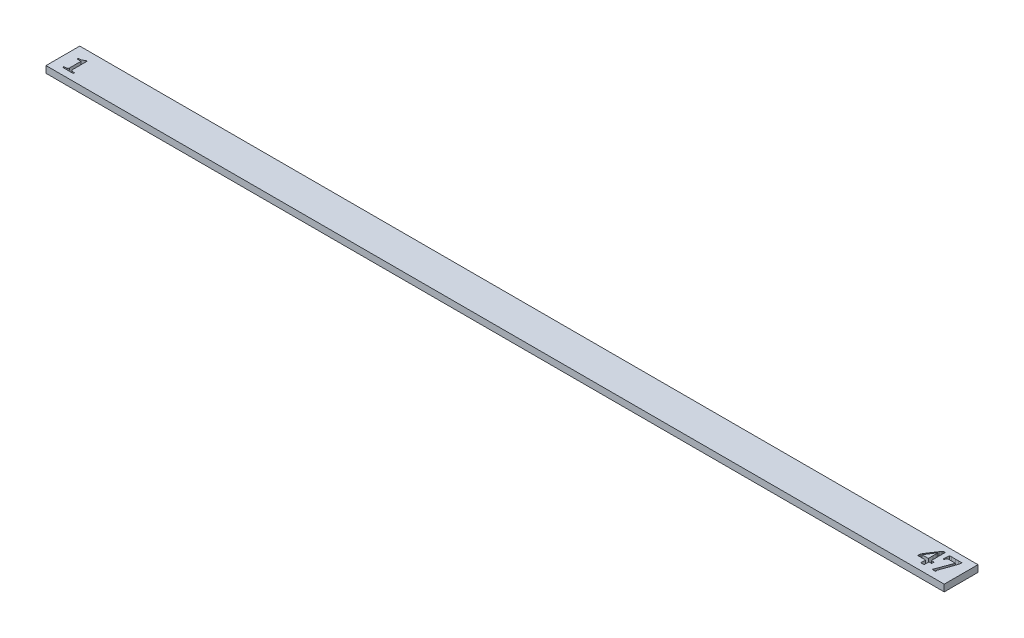
SolidWorks part; units mm, degrees
ref_plane "Front Plane" through (0, 0, 0) normal (0, 0, 1) x (1, 0, 0)
ref_plane "Top Plane" through (0, 0, 0) normal (0, 1, 0) x (1, 0, 0)
ref_plane "Right Plane" through (0, 0, 0) normal (1, 0, 0) x (0, 0, -1)
sketch "Sketch1" plane through (0, 0, 0) normal (0, 1, 0) x (1, 0, 0)
  line L1 (0, 0) -> (399, 0)
  line L2 (0, 0) -> (0, 15)
  line L3 (0, 15) -> (399, 15)
  line L4 (399, 0) -> (399, 15)
  dimension "D1" = 399
  dimension "D2" = 15
extrude "Boss-Extrude1" add sketch "Sketch1" along normal blind 3 contours L2 L1 L4 L3
sketch "Sketch3" plane through (0, 3, 0) normal (0, 1, 0) x (1, 0, 0)
  line L0 (0, 3) -> (399, 3)
  line L1 (0, 0) -> (0, 15) construction
  line L2 (399, 0) -> (399, 15) construction
  line L3 (0, 0) -> (399, 0) construction
  line L4 (390.1574, 12.1343) -> (391.8617, 12.1196)
  line L5 (391.8617, 12.1196) -> (393.3036, 12.1343)
  line L6 (393.3036, 12.1343) -> (394.1306, 12.1343)
  line L7 (394.1306, 12.1343) -> (394.416, 12.1343)
  line L8 (393.291, 7.2481) -> (392.9405, 6.2512)
  line L9 (392.6047, 5.3193) -> (392.0317, 3.7031)
  line L10 (392.0968, 2.7313) -> (391.9142, 2.7313)
  line L11 (391.9142, 2.7313) -> (391.3874, 2.7397)
  line L12 (391.507, 5.3046) -> (392.7642, 8.6943)
  line L13 (392.7642, 8.6943) -> (393.0791, 9.559)
  line L14 (392.2899, 10.5224) -> (391.2341, 10.5056)
  line L15 (391.2341, 10.5056) -> (390.3904, 10.5224)
  line L16 (388.2537, 6.2239) -> (388.2537, 5.1493)
  line L17 (387.0448, 4.9415) -> (387.0448, 4.5133)
  line L18 (387.0448, 4.5133) -> (387.0448, 4.0557)
  line L19 (387.0448, 4.0557) -> (387.0448, 3.7409)
  line L20 (387.0448, 2.7313) -> (386.4403, 2.7313)
  line L21 (386.4403, 2.7313) -> (386.0667, 2.7313)
  line L22 (385.8421, 2.7313) -> (385.7225, 2.7313)
  line L23 (385.5672, 2.7313) -> (385.5672, 4.1187)
  line L24 (385.5672, 4.1187) -> (385.5672, 5.0128)
  line L25 (384.5408, 5.1493) -> (384.0686, 5.1493)
  line L26 (382.0746, 5.1493) -> (382.0746, 5.2206)
  line L27 (382.0746, 5.2206) -> (382.0746, 5.6719)
  line L28 (382.0746, 5.6719) -> (382.0746, 5.8167)
  line L29 (382.0746, 5.8167) -> (382.0746, 6.0854)
  line L30 (382.0746, 6.0854) -> (382.0746, 6.1378)
  line L31 (382.4944, 6.9984) -> (384.1504, 9.559)
  line L32 (387.0448, 12.382) -> (387.0448, 12.2938)
  line L33 (387.0448, 12.2938) -> (387.0448, 11.746)
  line L34 (387.0448, 11.746) -> (387.0448, 11.555)
  line L35 (387.0448, 11.555) -> (387.0448, 11.2507)
  line L36 (387.0448, 11.2507) -> (387.0448, 10.9485)
  line L37 (387.0448, 10.9485) -> (387.0448, 10.216)
  line L38 (387.0448, 10.216) -> (387.0448, 9.899)
  line L39 (387.0448, 9.899) -> (387.0448, 9.4834)
  line L40 (387.0448, 9.4834) -> (387.0448, 9.0993)
  line L41 (387.0448, 9.0993) -> (387.0448, 8.5746)
  line L42 (387.0448, 8.5746) -> (387.0448, 8.073)
  line L43 (387.0448, 8.073) -> (387.0448, 7.4874)
  line L44 (387.0448, 7.4874) -> (387.0448, 6.2239)
  line L45 (387.7059, 6.2239) -> (387.8885, 6.2239)
  line L46 (385.5672, 7.4307) -> (385.5672, 7.9953)
  line L47 (385.5672, 7.9953) -> (385.5672, 8.4802)
  line L48 (385.5672, 8.4802) -> (385.5735, 9.7332)
  line L49 (385.5735, 9.7332) -> (385.5672, 10.3062)
  line L50 (384.5933, 9.2778) -> (383.9489, 8.2346)
  line L51 (383.1283, 6.3582) -> (383.4788, 6.3582)
  line L52 (383.4788, 6.3582) -> (384.1777, 6.3582)
  line L53 (384.1777, 6.3582) -> (385.1516, 6.3582)
  line L54 (385.1516, 6.3582) -> (385.5672, 6.3582)
  spline S0 degree 3 poles (389.2885, 12.1343) (389.4074, 12.1343) (389.6971, 12.1343) (389.9867, 12.1343) (390.1574, 12.1343) knots 0 0 0 0 0.410628 1 1 1 1
  spline S1 degree 2 poles (394.416, 12.1343) (394.5483, 12.1343) (394.6805, 12.1343) knots 0 0 0 1 1 1
  spline S2 degree 2 poles (394.6805, 12.1343) (394.7016, 11.9249) (394.7015, 11.7146) knots 0 0 0 1 1 1
  spline S3 degree 3 poles (394.7015, 11.7146) (394.7031, 11.6686) (394.6907, 11.5918) (394.6741, 11.4778) (394.6522, 11.3659) (394.6251, 11.2364) (394.5773, 11.0283) (394.5357, 10.8643) (394.5063, 10.7491) knots 0 0 0 0 0.13905 0.235946 0.350701 0.485483 0.638259 1 1 1 1
  spline S4 degree 3 poles (394.5063, 10.7491) (394.3713, 10.3858) (394.2226, 9.9355) (394.055, 9.4149) (393.9732, 9.1593) (393.9146, 8.9873) (393.8766, 8.8853) knots 0 0 0 0 0.590758 0.723007 0.834001 1 1 1 1
  spline S5 degree 3 poles (393.8766, 8.8853) (393.8139, 8.7235) (393.7049, 8.4219) (393.6038, 8.1175) (393.5618, 7.9764) knots 0 0 0 0 0.54115 1 1 1 1
  spline S6 degree 3 poles (393.5618, 7.9764) (393.5158, 7.8672) (393.4261, 7.6242) (393.3365, 7.3811) (393.291, 7.2481) knots 0 0 0 0 0.457479 1 1 1 1
  spline S7 degree 3 poles (392.9405, 6.2512) (392.9019, 6.129) (392.7893, 5.8185) (392.6773, 5.5079) (392.6047, 5.3193) knots 0 0 0 0 0.387978 1 1 1 1
  spline S8 degree 2 poles (392.0317, 3.7031) (391.9708, 3.5883) (391.9583, 3.4597) knots 0 0 0 1 1 1
  spline S9 degree 3 poles (391.9583, 3.4597) (391.9594, 3.4188) (391.9839, 3.3553) (392.0515, 3.2864) (392.1193, 3.235) (392.1889, 3.1853) (392.257, 3.1186) (392.2825, 3.0565) (392.2836, 3.0168) knots 0 0 0 0 0.21312 0.343422 0.503307 0.660927 0.793754 1 1 1 1
  spline S10 degree 3 poles (392.2836, 3.0168) (392.2823, 2.9669) (392.2381, 2.8546) (392.1492, 2.7737) (392.0968, 2.7313) knots 0 0 0 0 0.419347 1 1 1 1
  spline S11 degree 3 poles (391.3874, 2.7397) (391.3602, 2.7429) (391.309, 2.7411) (391.2271, 2.7429) (391.065, 2.7317) (390.9263, 2.7344) (390.8186, 2.7313) knots 0 0 0 0 0.143976 0.269387 0.431851 1 1 1 1
  spline S12 degree 2 poles (390.8186, 2.7313) (390.6779, 2.7313) (390.5373, 2.7313) knots 0 0 0 1 1 1
  spline S13 degree 3 poles (390.5373, 2.7313) (390.5497, 2.8378) (390.636, 3.1077) (390.7523, 3.3648) (390.8249, 3.5247) knots 0 0 0 0 0.377761 1 1 1 1
  spline S14 degree 3 poles (390.8249, 3.5247) (390.8592, 3.6042) (390.917, 3.7399) (390.9975, 3.9457) (391.0768, 4.1509) (391.1699, 4.3903) (391.3144, 4.7787) (391.4266, 5.0879) (391.507, 5.3046) knots 0 0 0 0 0.13619 0.232079 0.347806 0.482346 0.636339 1 1 1 1
  spline S15 degree 3 poles (393.0791, 9.559) (393.1161, 9.6353) (393.1856, 9.8169) (393.2493, 10.0004) (393.2826, 10.1047) knots 0 0 0 0 0.436195 1 1 1 1
  spline S16 degree 3 poles (393.2826, 10.1047) (393.2964, 10.1557) (393.3489, 10.2789) (393.3843, 10.4082) (393.417, 10.4825) knots 0 0 0 0 0.394055 1 1 1 1
  spline S17 degree 3 poles (393.417, 10.4825) (393.2072, 10.4941) (392.8316, 10.5116) (392.4558, 10.5235) (392.2899, 10.5224) knots 0 0 0 0 0.558859 1 1 1 1
  spline S18 degree 3 poles (390.3904, 10.5224) (390.2795, 10.5191) (390.1233, 10.5162) (389.9439, 10.4576) (389.8479, 10.402) (389.7801, 10.3185) (389.7259, 10.2157) (389.6823, 10.0881) (389.6537, 9.9447) (389.6276, 9.8052) (389.598, 9.6861) (389.5621, 9.5983) (389.5277, 9.5316) (389.4769, 9.4939) (389.3959, 9.4512) (389.3197, 9.4525) (389.2696, 9.4478) knots 0 0 0 0 0.189213 0.259177 0.317619 0.373826 0.438412 0.513621 0.600884 0.685342 0.753932 0.807539 0.846294 0.87826 0.912652 1 1 1 1
  spline S19 degree 3 poles (389.2696, 9.4478) (389.2096, 9.4441) (389.0726, 9.511) (389.0612, 9.6645) (389.0597, 9.7332) knots 0 0 0 0 0.447089 1 1 1 1
  spline S20 degree 3 poles (389.0597, 9.7332) (389.0577, 9.8826) (389.0859, 10.2424) (389.1123, 10.6021) (389.1395, 10.812) knots 0 0 0 0 0.413664 1 1 1 1
  spline S21 degree 3 poles (389.1395, 10.812) (389.1743, 11.0497) (389.212, 11.4917) (389.2566, 11.9331) (389.2885, 12.1343) knots 0 0 0 0 0.541005 1 1 1 1
  spline S22 degree 3 poles (388.2537, 5.1493) (388.1313, 5.1493) (387.9158, 5.1493) (387.7003, 5.1493) (387.6073, 5.1493) knots 0 0 0 0 0.568182 1 1 1 1
  spline S23 degree 2 poles (387.6073, 5.1493) (387.326, 5.1493) (387.0448, 5.1493) knots 0 0 0 1 1 1
  spline S24 degree 3 poles (387.0448, 5.1493) (387.0448, 5.1031) (387.0448, 5.0338) (387.0448, 4.9646) (387.0448, 4.9415) knots 0 0 0 0 0.666667 1 1 1 1
  spline S25 degree 3 poles (387.0448, 3.7409) (387.0448, 3.6905) (387.0448, 3.5471) (387.0448, 3.4037) (387.0448, 3.3106) knots 0 0 0 0 0.35122 1 1 1 1
  spline S26 degree 3 poles (387.0448, 3.3106) (387.0448, 3.2302) (387.0448, 3.0371) (387.0448, 2.844) (387.0448, 2.7313) knots 0 0 0 0 0.416667 1 1 1 1
  spline S27 degree 2 poles (386.0667, 2.7313) (385.9544, 2.7313) (385.8421, 2.7313) knots 0 0 0 1 1 1
  spline S28 degree 2 poles (385.7225, 2.7313) (385.6448, 2.7313) (385.5672, 2.7313) knots 0 0 0 1 1 1
  spline S29 degree 2 poles (385.5672, 5.0128) (385.5672, 5.081) (385.5672, 5.1493) knots 0 0 0 1 1 1
  spline S30 degree 3 poles (385.5672, 5.1493) (385.4244, 5.1493) (385.0823, 5.1493) (384.7402, 5.1493) (384.5408, 5.1493) knots 0 0 0 0 0.417178 1 1 1 1
  spline S31 degree 2 poles (384.0686, 5.1493) (383.3906, 5.1493) (382.7127, 5.1493) knots 0 0 0 1 1 1
  spline S32 degree 3 poles (382.7127, 5.1493) (382.6476, 5.1493) (382.5448, 5.1493) (382.4419, 5.1493) (382.4042, 5.1493) knots 0 0 0 0 0.632653 1 1 1 1
  spline S33 degree 2 poles (382.4042, 5.1493) (382.2394, 5.1493) (382.0746, 5.1493) knots 0 0 0 1 1 1
  spline S34 degree 3 poles (382.0746, 6.1378) (382.1238, 6.2444) (382.1936, 6.3963) (382.2862, 6.5855) (382.3422, 6.7026) (382.3904, 6.8013) (382.4392, 6.8983) (382.4714, 6.9628) (382.4944, 6.9984) knots 0 0 0 0 0.367667 0.523514 0.659761 0.774436 0.867544 1 1 1 1
  spline S35 degree 3 poles (384.1504, 9.559) (384.3071, 9.8063) (384.5391, 10.1441) (384.8248, 10.5655) (385.0022, 10.8076) (385.1506, 11.0139) (385.3031, 11.2258) (385.4004, 11.3743) (385.4559, 11.4648) knots 0 0 0 0 0.379956 0.532152 0.660989 0.769655 0.862163 1 1 1 1
  spline S36 degree 3 poles (385.4559, 11.4648) (385.5184, 11.5621) (385.622, 11.7417) (385.7461, 11.9077) (385.8001, 11.9811) knots 0 0 0 0 0.559034 1 1 1 1
  spline S37 degree 3 poles (385.8001, 11.9811) (385.8589, 12.0632) (385.9619, 12.1904) (386.0501, 12.3281) (386.0814, 12.382) knots 0 0 0 0 0.618512 1 1 1 1
  spline S38 degree 3 poles (386.0814, 12.382) (386.188, 12.3822) (386.3512, 12.402) (386.5152, 12.4001) (386.5725, 12.403) knots 0 0 0 0 0.649821 1 1 1 1
  spline S39 degree 3 poles (386.5725, 12.403) (386.6326, 12.4002) (386.7904, 12.4025) (386.9473, 12.383) (387.0448, 12.382) knots 0 0 0 0 0.381894 1 1 1 1
  spline S40 degree 2 poles (387.0448, 6.2239) (387.3753, 6.2239) (387.7059, 6.2239) knots 0 0 0 1 1 1
  spline S41 degree 2 poles (387.8885, 6.2239) (388.0711, 6.2239) (388.2537, 6.2239) knots 0 0 0 1 1 1
  spline S42 degree 3 poles (385.5672, 6.3582) (385.5672, 6.4639) (385.5672, 6.6451) (385.5672, 6.8263) (385.5672, 6.9018) knots 0 0 0 0 0.583012 1 1 1 1
  spline S43 degree 3 poles (385.5672, 6.9018) (385.5672, 6.9921) (385.5672, 7.1124) (385.5672, 7.2572) (385.5672, 7.3433) (385.5672, 7.3993) (385.5672, 7.4307) knots 0 0 0 0 0.511905 0.68254 0.821429 1 1 1 1
  spline S44 degree 3 poles (385.5672, 10.3062) (385.5654, 10.3469) (385.5754, 10.46) (385.576, 10.5736) (385.5819, 10.6462) knots 0 0 0 0 0.357984 1 1 1 1
  spline S45 degree 2 poles (385.5819, 10.6462) (385.4879, 10.5109) (385.3804, 10.386) knots 0 0 0 1 1 1
  spline S46 degree 2 poles (385.3804, 10.386) (385.3063, 10.2569) (385.2167, 10.1383) knots 0 0 0 1 1 1
  spline S47 degree 3 poles (385.2167, 10.1383) (385.1149, 10.0112) (384.9005, 9.729) (384.6991, 9.4374) (384.5933, 9.2778) knots 0 0 0 0 0.459339 1 1 1 1
  spline S48 degree 2 poles (383.9489, 8.2346) (383.8415, 8.0668) (383.7411, 7.8946) knots 0 0 0 1 1 1
  spline S49 degree 3 poles (383.7411, 7.8946) (383.5913, 7.6473) (383.2622, 7.1508) (382.9554, 6.6391) (382.8302, 6.3582) knots 0 0 0 0 0.485064 1 1 1 1
  spline S50 degree 3 poles (382.8302, 6.3582) (382.8918, 6.3582) (382.9911, 6.3582) (383.0905, 6.3582) (383.1283, 6.3582) knots 0 0 0 0 0.619718 1 1 1 1
  point P8 (0, 0)
  dimension "D1" = 3
sketch "Sketch6" plane through (0, 3, 0) normal (0, 1, 0) x (1, 0, 0)
  line L0 (9.0667, 3) -> (4.4, 3)
  line L1 (4.4, 3) -> (4.4, 3.5333)
  line L2 (6.1333, 4.4021) -> (6.1333, 9.4)
  line L3 (6.1333, 9.4) -> (4.4, 9.4)
  line L4 (4.4, 9.4) -> (4.4, 9.9333)
  line L5 (4.4, 9.9333) -> (4.7708, 9.9333)
  line L6 (6.9063, 10.8667) -> (7.4667, 10.8667)
  line L7 (7.4667, 8.6813) -> (7.4667, 4.4771)
  line L8 (9.0667, 3.5333) -> (9.0667, 3)
  spline S0 degree 3 poles (4.4, 3.5333) (4.4906, 3.5373) (4.6409, 3.5544) (4.8612, 3.5732) (5.0605, 3.5939) (5.2574, 3.6135) (5.4646, 3.6453) (5.603, 3.6659) (5.6813, 3.6896) knots 0 0 0 0 0.21039 0.351267 0.513318 0.675537 0.810763 1 1 1 1
  spline S1 degree 3 poles (5.6813, 3.6896) (5.7489, 3.7133) (5.8461, 3.7566) (5.9542, 3.8436) (6.0199, 3.9204) (6.0747, 4.0123) (6.1218, 4.1744) (6.1362, 4.3073) (6.1333, 4.4021) knots 0 0 0 0 0.235251 0.343488 0.451439 0.564461 0.690935 1 1 1 1
  spline S2 degree 3 poles (4.7708, 9.9333) (5.0033, 9.9326) (5.3457, 9.9689) (5.7802, 10.0922) (6.0742, 10.2224) (6.34, 10.3701) (6.6302, 10.5692) (6.8142, 10.7396) (6.9063, 10.8667) knots 0 0 0 0 0.289649 0.426683 0.561658 0.689593 0.805376 1 1 1 1
  spline S3 degree 3 poles (7.4667, 10.8667) (7.4667, 10.7) (7.4667, 10.4403) (7.4667, 10.0806) (7.4667, 9.5188) (7.4667, 9.05) (7.4667, 8.6813) knots 0 0 0 0 0.228789 0.35653 0.493804 1 1 1 1
  spline S4 degree 3 poles (7.4667, 4.4771) (7.4652, 4.3238) (7.5089, 4.1322) (7.6276, 3.9406) (7.7255, 3.8361) (7.8135, 3.7747) (7.8792, 3.7458) knots 0 0 0 0 0.518336 0.640812 0.758815 1 1 1 1
  spline S5 degree 3 poles (7.8792, 3.7458) (7.9543, 3.7133) (8.0861, 3.6778) (8.2812, 3.6344) (8.4608, 3.6037) (8.6413, 3.5752) (8.8434, 3.5503) (8.9822, 3.5352) (9.0667, 3.5333) knots 0 0 0 0 0.202205 0.337958 0.495327 0.653832 0.79092 1 1 1 1
extrude "Cut-Extrude3" cut sketch "Sketch6" against normal blind 3
extrude "Cut-Extrude4" cut sketch "Sketch3" against normal through all both and the other way through all contours S21 S20 S19 S18 L15 L14 S17 S16 S15 L13 L12 S14 S13 L0 S10 S9 S8 L9 S7 L8 S6 S5 S4 S3 S2 S1 L7 L6 L5 L4 S0 | S41 L45 S40 L44 L43 L42 L41 L40 L39 L38 L37 L36 L35 L34 L33 L32 S39 S38 S37 S36 S35 L31 S34 L30 L29 L28 L27 L26 S33 S32 S31 L25 S30 S29 L24 L23 L0 S26 S25 L19 L18 L17 S24 S23 S22 L16 S50 S49 S48 L50
